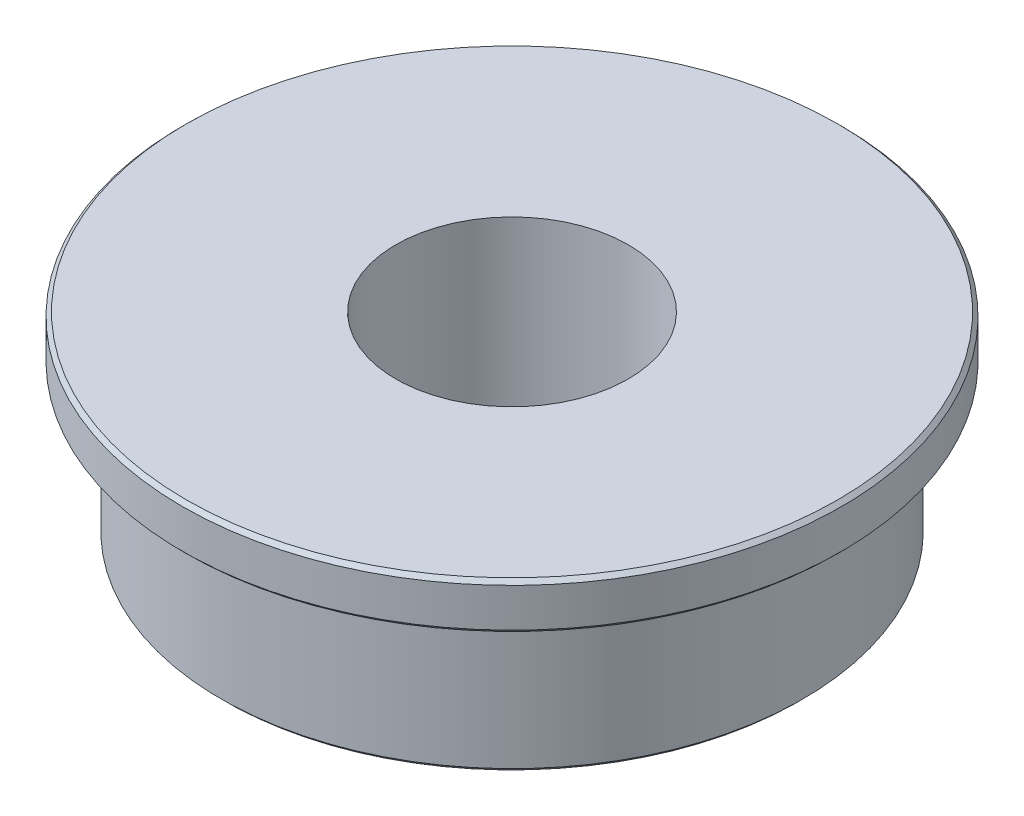
SolidWorks part; units mm, degrees
material "1060 合金"
ref_plane "前视基准面" through (0, 0, 0) normal (0, 0, 1) x (1, 0, 0)
ref_plane "上视基准面" through (0, 0, 0) normal (0, 1, 0) x (1, 0, 0)
ref_plane "右视基准面" through (0, 0, 0) normal (1, 0, 0) x (0, 0, -1)
sketch "草图1" plane through (0, 0, 0) normal (0, 0, 1) x (1, 0, 0)
  line L0 (3, 0) -> (3, 5)
  line L1 (3, 5) -> (8.5, 5)
  line L2 (8.5, 5) -> (8.5, 3.8)
  line L3 (8.5, 3.8) -> (7.5, 3.8)
  line L4 (7.5, 3.8) -> (7.5, 0)
  line L5 (7.5, 0) -> (3, 0)
  line L6 (0, 0) -> (0, 5.9585) construction
  dimension "D1" = 3
  dimension "D2" = 8.5
  dimension "D3" = 7.5
  dimension "D4" = 5
  dimension "D5" = 1.2
revolve "旋转1" add sketch "草图1" angle 360 about L6
chamfer "倒角1" distance 0.1 angle 45 3 edges at (0, 0, -7.5) (0, 3.8, -8.5) (0, 5, -8.5)
